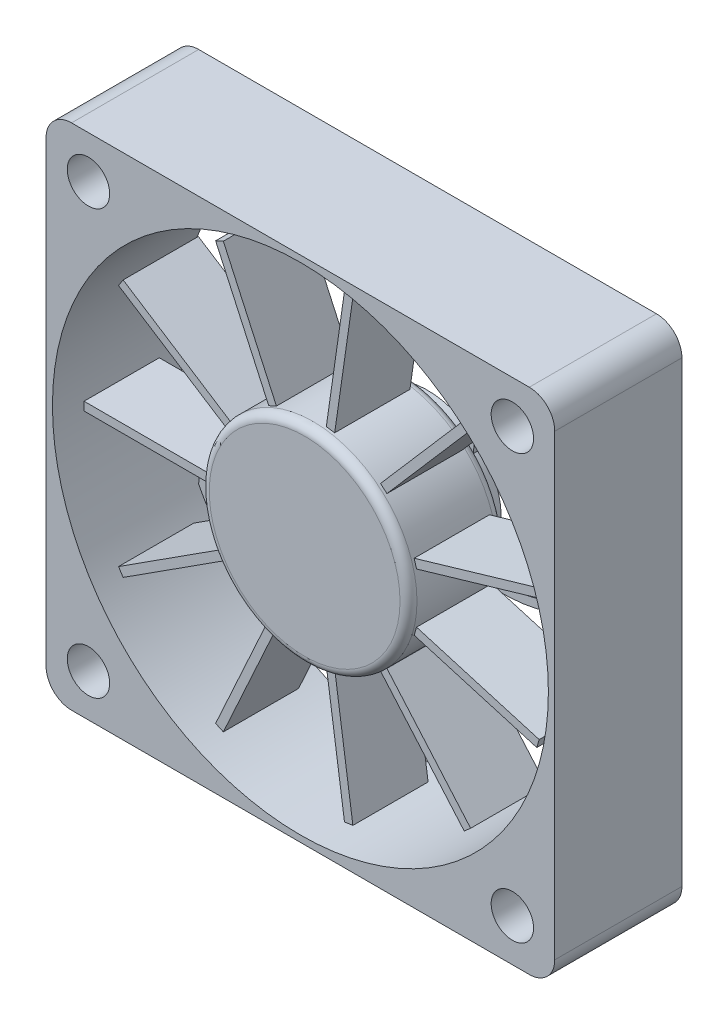
SolidWorks part; units mm, degrees
ref_plane "Front Plane" through (0, 0, 0) normal (0, 0, 1) x (1, 0, 0)
ref_plane "Top Plane" through (0, 0, 0) normal (0, 1, 0) x (1, 0, 0)
ref_plane "Right Plane" through (0, 0, 0) normal (1, 0, 0) x (0, 0, -1)
sketch "Sketch1" plane through (0, 0, 0) normal (0, 0, 1) x (1, 0, 0)
  line L1 (27, -30) -> (-27, -30)
  line L2 (30, -27) -> (30, 27)
  line L3 (27, 30) -> (-27, 30)
  line L4 (-30, -27) -> (-30, 27)
  line L5 (30, -30) -> (-30, 30) construction
  line L6 (30, 30) -> (-30, -30) construction
  line L7 (25, -25) -> (-25, -25) construction
  line L8 (25, -25) -> (25, 25) construction
  line L9 (25, 25) -> (-25, 25) construction
  line L10 (-25, -25) -> (-25, 25) construction
  line L11 (25, -25) -> (-25, 25) construction
  line L12 (25, 25) -> (-25, -25) construction
  arc A0 (30, 27) -> (27, 30) centre (27, 27) ccw
  arc A1 (27, -30) -> (30, -27) centre (27, -27) ccw
  arc A2 (-30, -27) -> (-27, -30) centre (-27, -27) ccw
  arc A3 (-30, 27) -> (-27, 30) centre (-27, 27) cw
  circle A4 centre (0, 0) radius 29.25
  circle A5 centre (-25, -25) radius 2.5
  circle A6 centre (25, -25) radius 2.5
  circle A7 centre (25, 25) radius 2.5
  circle A8 centre (-25, 25) radius 2.5
  point P0 (0, 0)
  dimension "D2" = 3
  dimension "D3" = 58.5
  dimension "D5" = 5
  dimension "D1" = 60
  dimension "D4" = 50
extrude "Boss-Extrude1" add sketch "Sketch1" along normal blind 15
sketch "Sketch2" plane through (0, 0, 0) normal (0, 0, -1) x (-1, 0, 0)
  line L0 (-25.9003, 22.1541) -> (-24.9027, 22.0852)
  line L1 (22.1541, 25.9003) -> (22.0852, 24.9027)
  line L2 (25.9003, -22.1541) -> (24.9027, -22.0852)
  line L3 (-22.1541, -25.9003) -> (-22.0852, -24.9027)
  arc A0 (-5.8972, -6.3816) -> (5.4833, -6.7405) centre (0, 0) ccw
  arc A1 (5.8972, 6.3816) -> (-5.4833, 6.7405) centre (0, 0) ccw
  arc A2 (-6.3816, 5.8972) -> (-6.7405, -5.4833) centre (0, 0) ccw
  arc A3 (6.3816, -5.8972) -> (6.7405, 5.4833) centre (0, 0) ccw
  spline S0 degree 3 poles (-24.9027, 22.0852) (-26.2816, 2.1138) (-20.2276, -7.0757) (-6.7405, -5.4833) knots 0 0 0 0 0.983104 0.983104 0.983104 0.983104
  spline S2 degree 2 poles (-25.9003, 22.1541) (-26.7241, 10.6216) (-22.899, 0.0728) (-19.2329, -3.8625) (-15.5017, -5.8845) (-9.9589, -6.9703) (-5.8972, -6.3816) knots 0 0 0 0.375 0.5625 0.6875 0.8125 1 1 1
  spline S3 degree 3 poles (22.0852, 24.9027) (2.1138, 26.2816) (-7.0757, 20.2276) (-5.4833, 6.7405) knots 0 0 0 0 0.983104 0.983104 0.983104 0.983104
  spline S4 degree 2 poles (22.1541, 25.9003) (10.6216, 26.7241) (0.0728, 22.899) (-3.8625, 19.2329) (-5.8845, 15.5017) (-6.9703, 9.9589) (-6.3816, 5.8972) knots 0 0 0 0.375 0.5625 0.6875 0.8125 1 1 1
  spline S5 degree 3 poles (24.9027, -22.0852) (26.2816, -2.1138) (20.2276, 7.0757) (6.7405, 5.4833) knots 0 0 0 0 0.983104 0.983104 0.983104 0.983104
  spline S6 degree 2 poles (25.9003, -22.1541) (26.7241, -10.6216) (22.899, -0.0728) (19.2329, 3.8625) (15.5017, 5.8845) (9.9589, 6.9703) (5.8972, 6.3816) knots 0 0 0 0.375 0.5625 0.6875 0.8125 1 1 1
  spline S7 degree 3 poles (-22.0852, -24.9027) (-2.1138, -26.2816) (7.0757, -20.2276) (5.4833, -6.7405) knots 0 0 0 0 0.983104 0.983104 0.983104 0.983104
  spline S8 degree 2 poles (-22.1541, -25.9003) (-10.6216, -26.7241) (-0.0728, -22.899) (3.8625, -19.2329) (5.8845, -15.5017) (6.9703, -9.9589) (6.3816, -5.8972) knots 0 0 0 0.375 0.5625 0.6875 0.8125 1 1 1
  point P25 (0, 0)
  dimension "D2" = 4
extrude "Boss-Extrude2" add sketch "Sketch2" against normal blind 1
sketch "Sketch3" plane through (0, 0, 1) normal (0, 0, 1) x (1, 0, 0)
  circle A0 centre (0, 0) radius 2
  dimension "D1" = 4
extrude "Boss-Extrude3" add sketch "Sketch3" along normal blind 2
sketch "Sketch4" plane through (0, 0, 3) normal (0, 0, 1) x (1, 0, 0)
  circle A0 centre (0, 0) radius 12.25
  dimension "D1" = 24.5
extrude "Boss-Extrude4" add sketch "Sketch4" along normal offset from surface (11.5 mm away) 0.5 up to face at (27.5, 25, 15)
fillet "Fillet1" radius 1 2 edges at (12.25, 0, 3) (12.25, 0, 14.5)
sketch "Sketch5" plane through (0, 0, 0) normal (0, 1, 0) x (1, 0, 0)
  line L0 (-12.25, -4) -> (-12.25, -13.5) construction
  line L1 (-12.25, -4.3203) -> (-27.3266, -4.3203)
  line L2 (-12.25, -4.3203) -> (-12.25, -13.1951)
  line L3 (-12.25, -13.1951) -> (-27.3266, -13.1951)
  line L4 (-27.3266, -4.3203) -> (-27.3266, -13.1951)
extrude "Boss-Extrude5" add sketch "Sketch5" along normal mid plane 1 separate body
pattern_circular "CirPattern3" count 11 over 360 about axis through (0, 0, 0) along (0, 0, 1) of bodies 105
